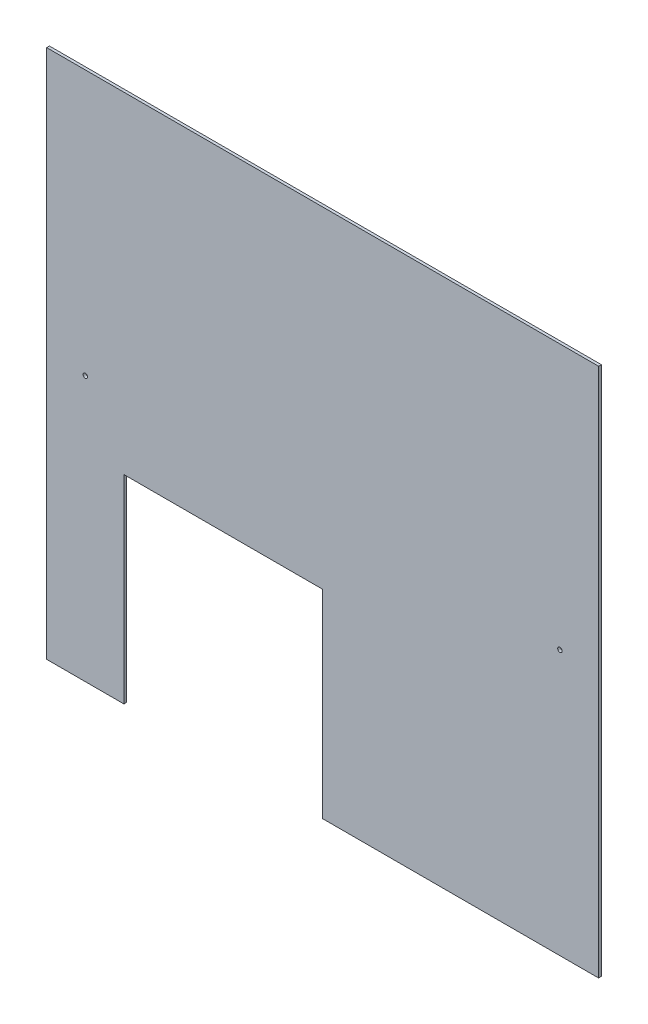
SolidWorks part; units mm, degrees
ref_plane "Front Plane" through (0, 0, 0) normal (0, 0, 1) x (1, 0, 0)
ref_plane "Top Plane" through (0, 0, 0) normal (0, 1, 0) x (1, 0, 0)
ref_plane "Right Plane" through (0, 0, 0) normal (1, 0, 0) x (0, 0, -1)
sketch "Sketch1" plane through (0, 0, 0) normal (0, 0, 1) x (1, 0, 0)
  line L0 (-218.244, -432.285) -> (-218.244, -203.685)
  line L1 (-307.144, 177.315) -> (327.856, 177.315)
  line L2 (-307.144, 177.315) -> (-307.144, -432.285)
  line L3 (-307.144, -432.285) -> (-218.244, -432.285)
  line L4 (327.856, 177.315) -> (327.856, -432.285)
  line L5 (-218.244, -203.685) -> (10.356, -203.685)
  line L6 (10.356, -203.685) -> (10.356, -432.285)
  line L7 (10.356, -432.285) -> (327.856, -432.285)
  point P4 (10.356, -432.285)
  dimension "D1" = 635
  dimension "D2" = 609.6
  dimension "D3" = 88.9
  dimension "D4" = 228.6
  dimension "D5" = 381
extrude "Boss-Extrude1" add sketch "Sketch1" along normal blind 3.175
sketch "Sketch2" plane through (0, 0, 3.175) normal (0, 0, 1) x (1, 0, 0)
  line L0 (-307.144, -432.285) -> (-218.244, -432.285) construction
  line L1 (10.356, -432.285) -> (327.856, -432.285) construction
  line L2 (327.856, -432.285) -> (327.856, 177.315) construction
  line L3 (-307.144, 177.315) -> (-307.144, -432.285) construction
  circle A0 centre (-262.694, -127.485) radius 2.5797
  circle A1 centre (283.406, -127.485) radius 2.5797
  dimension "D5" = 5.1594
  dimension "D6" = 5.1594
  dimension "D1" = 304.8
  dimension "D2" = 304.8
  dimension "D3" = 44.45
  dimension "D4" = 44.45
extrude "Cut-Extrude1" cut sketch "Sketch2" against normal blind 3.175
